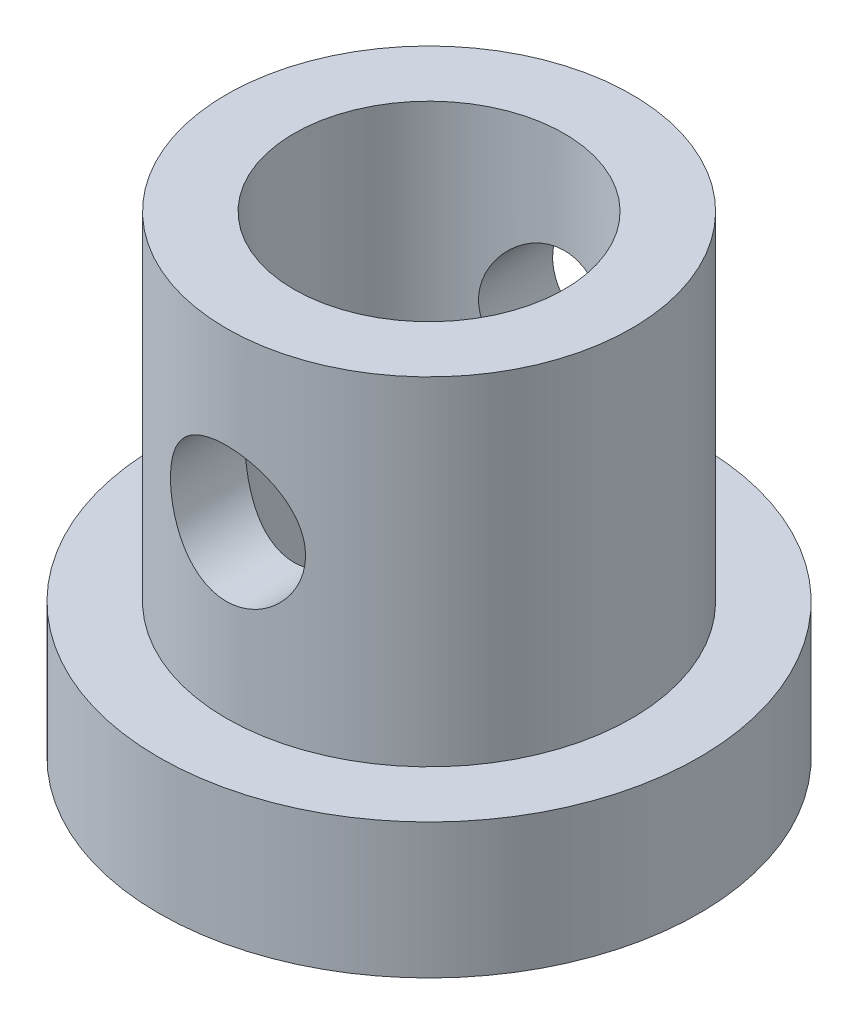
SolidWorks part; units mm, degrees
ref_plane "Front Plane" through (0, 0, 0) normal (0, 0, 1) x (1, 0, 0)
ref_plane "Top Plane" through (0, 0, 0) normal (0, 1, 0) x (1, 0, 0)
ref_plane "Right Plane" through (0, 0, 0) normal (1, 0, 0) x (0, 0, -1)
sketch "Sketch1" plane through (0, 0, 0) normal (0, 1, 0) x (1, 0, 0)
  circle A0 centre (0, 0) radius 2
  circle A1 centre (0, 0) radius 4
  dimension "D1" = 8
  dimension "D2" = 4
extrude "Boss-Extrude1" add sketch "Sketch1" along normal blind 2
sketch "Sketch2" plane through (0, 2, 0) normal (0, 1, 0) x (1, 0, 0)
  circle A0 centre (0, 0) radius 3
  circle A1 centre (0, 0) radius 2 construction
  circle A2 centre (0, 0) radius 2
  dimension "D1" = 6
extrude "Boss-Extrude2" add sketch "Sketch2" along normal blind 5
sketch "Sketch3" plane through (0, 0, 0) normal (0, 0, 1) x (1, 0, 0)
  line L0 (3, 7) -> (-3, 7) construction
  circle A0 centre (0, 4.5) radius 1
  dimension "D2" = 2
  dimension "D1" = 2.5
extrude "Cut-Extrude1" cut sketch "Sketch3" against normal mid plane 25
